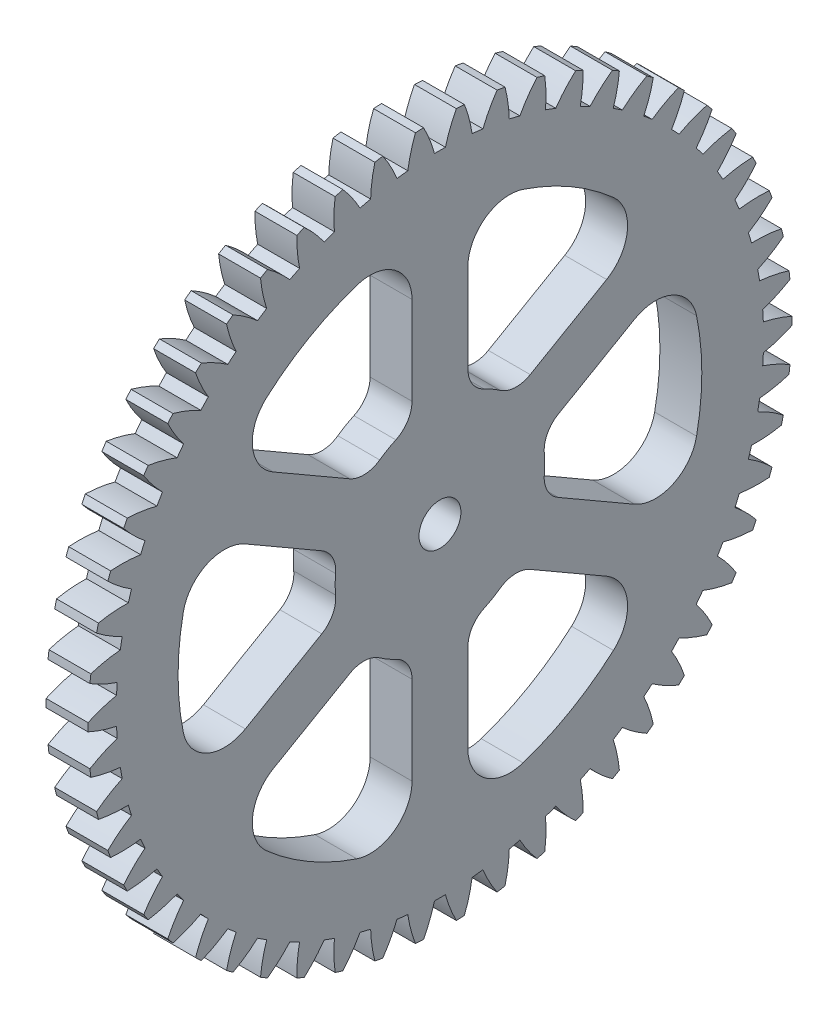
SolidWorks part; units mm, degrees
ref_plane "Plane1" through (0, 0, 0) normal (0, 0, 1) x (1, 0, 0)
ref_plane "Plane2" through (0, 0, 0) normal (0, 1, 0) x (1, 0, 0)
ref_plane "Plane3" through (0, 0, 0) normal (1, 0, 0) x (0, 0, -1)
sketch "HoldingSke" plane through (0, 0, 0) normal (0, 1, 0) x (1, 0, 0)
  line L0 (0, 0) -> (0.6531, -0.8989)
  line L1 (-15, 0) -> (100, 0) construction
  line L2 (0, 0) -> (-2.1039, 2.3779)
  line L3 (0, 0) -> (-11.863, 4.5341)
  line L4 (0, 0) -> (5.0761, 6.9867)
  line L5 (0, 0) -> (-46.8476, -17.4728)
  line L6 (0, 0) -> (-2.4869, -1.6779)
  line L7 (-2.1039, 2.3779) -> (8.6588, 51.2066)
  line L8 (-76.2, 54.61) -> (-75.2, 54.61)
  line L9 (-71.009, 38.7566) -> (-53.1078, 45.2721)
  line L10 (-76.2, 71.12) -> (104.1128, 71.12)
  line L11 (0, 0) -> (-3, 0)
  line L12 (-76.2, 101.6) -> (-76.166, 101.6)
  line L13 (24.9733, 27.94) -> (52.9518, 28.4284)
  line L14 (24.9733, 27.94) -> (24.9743, 27.94)
  line L15 (24.9733, 27.94) -> (100.4006, 29.5858)
  line L16 (-63.627, -0.9) -> (-12.827, -0.9)
  circle A0 centre (0, 0) radius 3
  circle A1 centre (0, 0) radius 23.174
  circle A2 centre (0, 0) radius 37.5
  circle A3 centre (0, 0) radius 3
  dimension "MHD" = 46.348
  dimension "Hub_dia" = 75
  dimension "Bore" = 6
  dimension "MBD" = 6
  dimension "Num_teeth" = 54
  dimension "Pitch" = 1.1111
  dimension "Overall_len" = 50
  dimension "Show_teeth" = 54
  dimension "Thickness" = 3
  dimension "OAL" = 50.0008
  dimension "T_dim" = 1
  dimension "Ap" = 20
  dimension "H" = 19.05
  dimension "Pitch_radius" = 180.3128
  dimension "Width" = 3
  dimension "Backlash" = 0.034
  dimension "Addendum_fac" = 1
  dimension "Dedendum_fac" = 1.25
  dimension "Clearance_fac" = 0.25
  dimension "Dedendum_add" = 0.001
  dimension "Module" = 0.9
sketch "BasProSke" plane through (0, 0, 0) normal (0, 1, 0) x (1, 0, 0)
  line L0 (-10, 0) -> (60, 0) construction
  line L1 (0, 0) -> (0, 25.2)
  line L2 (0, 0) -> (3, 0)
  line L3 (3, 0) -> (3, 25.2)
  line L4 (3, 25.2) -> (0, 25.2)
  dimension "Thickness" = 3
  dimension "Diameter" = 50.4
revolve "Base-Revolve" add sketch "BasProSke" angle 360 about L0
sketch "TooCutSke" plane through (0, 0, 0) normal (1, 0, 0) x (0, 0, -1)
  line L1 (0, 0) -> (0, 107) construction
  line L2 (0, 0) -> (-0.7663, 24.2879) construction
  line L3 (0, 0) -> (-2.8248, 48.5006) construction
  line L4 (-0.7663, 24.2879) -> (-1.4124, 24.2503) construction
  arc A0 (0.3905, 23.1707) -> (-0.3905, 23.1707) centre (0, 0) ccw
  arc A1 (1.1907, 25.1973) -> (-1.1907, 25.1973) centre (0, 0) ccw
  circle A2 centre (0, 0) radius 24.3 construction
  circle A3 centre (0, 0) radius 22.8345 construction
  arc A4 (-0.3905, 23.1707) -> (-1.1907, 25.1973) centre (-9.7744, 20.6368) ccw
  arc A5 (1.1907, 25.1973) -> (0.3905, 23.1707) centre (9.7744, 20.6368) ccw
  dimension "Root_dia" = 46.348
  dimension "Overcut_dia" = 50.4508
  dimension "Pitch_dia" = 48.6
  dimension "Base_dia" = 45.6691
  dimension "Flank_rad" = 9.72
  dimension "Half_ang" = 3.333
  dimension "Half_CT" = 0.6473
extrude "ToothCut" cut sketch "TooCutSke" along normal through all
fillet "Breaks" [suppressed] radius 0.018
fillet "RootFillets" [suppressed] radius 0.226
pattern_circular "TeethCuts" count 54 every 6.667 about axis through (-10, 0, 0) along (1, 0, 0) of "ToothCut", "RootFillets", "Breaks"
sketch "HubNeaOneSke" plane through (0, 0, 0) normal (-1, 0, 0) x (0, 0, 1)
  circle A0 centre (0, 0) radius 23.174
  dimension "Diameter" = 46.348
extrude "HubNearOne" [suppressed] add sketch "HubNeaOneSke" along normal blind 47.0008
sketch "HubNeaBotSke" plane through (0, 0, 0) normal (-1, 0, 0) x (0, 0, 1)
  circle A0 centre (0, 0) radius 23.174
  dimension "Diameter" = 46.348
extrude "HubNearBoth" [suppressed] add sketch "HubNeaBotSke" along normal blind 23.5004
ref_plane "FarPln" through (3, 0, 0) normal (1, 0, 0) x (0, 0, -1)
sketch "HubFarSke" plane through (3, 0, 0) normal (1, 0, 0) x (0, 0, -1)
  circle A0 centre (0, 0) radius 23.174
  dimension "Diameter" = 46.348
extrude "HubFar" [suppressed] add sketch "HubFarSke" along normal blind 23.5004
sketch "KeySke" plane through (0, 0, 0) normal (1, 0, 0) x (0, 0, -1)
  line L0 (-1, 0) -> (-1, 4)
  line L1 (-1, 4) -> (1, 4)
  line L2 (1, 4) -> (1, 0)
  line L3 (0, 0) -> (0, 34) construction
  line L4 (-1, 0) -> (1, 0)
  dimension "Offset" = 4
  dimension "Width" = 2
extrude "Keyway" [suppressed] cut sketch "KeySke" along normal mid plane 100.0016
pattern_circular "Keyway2" [suppressed] count 2 every 90 about axis through (-10, 0, 0) along (1, 0, 0)
sketch "Sketch1" plane through (3, 0, 0) normal (1, 0, 0) x (0, 0, -1)
  circle A0 centre (0, 0) radius 1.5
  dimension "D1" = 3
extrude "Cut-Extrude1" cut sketch "Sketch1" against normal through all
sketch "Sketch2" plane through (3, 0, 0) normal (1, 0, 0) x (0, 0, -1)
  line L0 (-2, 18.643) -> (-2, 7.2284)
  line L3 (-5.26, 5.3463) -> (-15.1453, 11.0536)
  arc A1 (-2, 7.2284) -> (-5.26, 5.3463) centre (0, 0) ccw
  arc A2 (-2, 18.643) -> (-15.1453, 11.0536) centre (0, 0) ccw
  dimension "D1" = 37.5
  dimension "D3" = 15
  dimension "D4" = 2
extrude "Cut-Extrude2" cut sketch "Sketch2" against normal through all
fillet "Fillet1" radius 2 2 edges at (1.5, 5.3463, 5.26) (1.5, 7.2284, 2)
fillet "Fillet2" radius 3 2 edges at (1.5, 11.0536, 15.1453) (1.5, 18.643, 2)
pattern_circular "CirPattern2" count 6 every 60 about axis through (0, 0, 0) along (1, 0, 0) of "Fillet2", "Fillet1", "Cut-Extrude2"
equation "' \"Module@HoldingSke\" = 6.35"
equation "' \"Num_teeth@HoldingSke\" = 12"
equation "' \"Ap@HoldingSke\" =  20"
equation "' \"Ap@HoldingSke\" = 20"
equation "' \"Width@HoldingSke\" = 0.5 * 25.4"
equation "' \"Hub_dia@HoldingSke\"= 1 * 25.4"
equation "' \"Hub_dia@HoldingSke\" = 1 * 25.4"
equation "' \"Overall_len@HoldingSke\" = 1.0 * 25.4"
equation "' \"Bore@HoldingSke\" = 0.75 * 25.4"
equation "' \"T_dim@HoldingSke\" = 0.1 * 25.4"
equation "' \"Width@KeySke\" = 0.25 * 25.4"
equation "' \"Show_teeth@HoldingSke\" = 13"
equation "' \"Backlash@HoldingSke\" = 0.009 * 25.4"
equation "' \"Addendum_fac@HoldingSke\" = 1.0"
equation "' \"Dedendum_fac@HoldingSke\" = 1.25"
equation "' \"Dedendum_add@HoldingSke\" = 0.00005 * 25.4"
equation "' \"Clearance_fac@HoldingSke\" = 0.25"
equation "\"Pitch@HoldingSke\" = 1 / \"Module@HoldingSke\""
equation "\"Overcut_dia@TooCutSke\" = (\"Num_teeth@HoldingSke\" + 2 * \"Addendum_fac@HoldingSke\") / \"Pitch@HoldingSke\" + 0.002 * 25.4"
equation "\"Pitch_dia@TooCutSke\" = \"Num_teeth@HoldingSke\" / \"Pitch@HoldingSke\""
equation "\"Base_dia@TooCutSke\" = \"Num_teeth@HoldingSke\" / \"Pitch@HoldingSke\" * cos((\"Ap@HoldingSke\"  * 3.14159265 / 180))"
equation "\"Root_dia@TooCutSke\" = (\"Num_teeth@HoldingSke\" + 2) / \"Pitch@HoldingSke\" - 2 * (\"Addendum_fac@HoldingSke\" + \"Dedendum_fac@HoldingSke\") / \"Pitch@HoldingSke\" - \"Dedendum_add@HoldingSke\" * 2"
equation "\"Half_ang@TooCutSke\" = 180 / \"Num_teeth@HoldingSke\""
equation "\"Half_CT@TooCutSke\" = \"Num_teeth@HoldingSke\" / \"Pitch@HoldingSke\" * sin((3.14159265 / 2 / \"Num_teeth@HoldingSke\")) / 2 - 7 * \"Backlash@HoldingSke\" / 4"
equation "\"Flank_rad@TooCutSke\" = \"Num_teeth@HoldingSke\" / \"Pitch@HoldingSke\" / 5"
equation "\"Radius@RootFillets\" = \"Clearance_fac@HoldingSke\" / \"Pitch@HoldingSke\" + \"Dedendum_add@HoldingSke\""
equation "\"Break_rad@Breaks\" = 0.02 / \"Pitch@HoldingSke\""
equation "\"Thickness@HoldingSke\" = \"Width@HoldingSke\""
equation "\"OAL@HoldingSke\" = \"Thickness@HoldingSke\""
equation "\"MHD@HoldingSke\" = (\"Num_teeth@HoldingSke\" + 2) / \"Pitch@HoldingSke\" - 2 * (\"Addendum_fac@HoldingSke\" + \"Dedendum_fac@HoldingSke\")  / \"Pitch@HoldingSke\" - \"Dedendum_add@HoldingSke\" * 2"
equation "\"MBD@HoldingSke\" = (\"Num_teeth@HoldingSke\" + 2) / \"Pitch@HoldingSke\" - 2 * (\"Addendum_fac@HoldingSke\" + \"Dedendum_fac@HoldingSke\")  / \"Pitch@HoldingSke\" - \"Dedendum_add@HoldingSke\" * 2 - 0.002 * 25.4"
equation "\"MHD@HoldingSke\" = ((sgn( \"MHD@HoldingSke\" - \"Hub_dia@HoldingSke\" )-1)*( \"MHD@HoldingSke\" - \"Hub_dia@HoldingSke\" ))/-2+ \"Hub_dia@HoldingSke\""
equation "\"MBD@HoldingSke\" = ((sgn( \"MBD@HoldingSke\" - \"Bore@HoldingSke\" )-1)*( \"MBD@HoldingSke\" - \"Bore@HoldingSke\" ))/-2+ \"Bore@HoldingSke\""
equation "\"OAL@HoldingSke\" = ((sgn( \"OAL@HoldingSke\" - \"Overall_len@HoldingSke\" )+1)*( \"OAL@HoldingSke\" - \"Overall_len@HoldingSke\" ))/2 + \"Overall_len@HoldingSke\" + 0.000002 * 25.4"
equation "\"Num_teeth@TeethCuts\" = int( \"Show_teeth@HoldingSke\" ) + 1"
equation "\"Num_teeth@TeethCuts\" = ((sgn( \"Num_teeth@TeethCuts\" - \"Num_teeth@HoldingSke\" )-1)*( \"Num_teeth@TeethCuts\" - \"Num_teeth@HoldingSke\" ))/-2+ \"Num_teeth@HoldingSke\""
equation "\"Num_teeth@TeethCuts\" = ((sgn( \"Num_teeth@TeethCuts\" - 2.0)+1)*( \"Num_teeth@TeethCuts\" - 2.0))/2 +2.0"
equation "\"Angle@TeethCuts\" = 360.0 / \"Num_teeth@HoldingSke\""
equation "\"Diameter@BasProSke\" = (\"Num_teeth@HoldingSke\" + 2 * \"Addendum_fac@HoldingSke\") / \"Pitch@HoldingSke\""
equation "\"Thickness@BasProSke\"  = \"Thickness@HoldingSke\""
equation "' \"Fillet_rad@BasProSke\" =  \"Thickness@HoldingSke\" * 0.05"
equation "' \"Fillet_rad@BasProSke\" = \"Thickness@HoldingSke\" * 0.05"
equation "\"MHD@HoldingSke\" = ((sgn( \"MHD@HoldingSke\" - \"Root_dia@TooCutSke\" )-1)*( \"MHD@HoldingSke\" - \"Root_dia@TooCutSke\" ))/-2+ \"Root_dia@TooCutSke\""
equation "\"Diameter@HubNeaOneSke\" = \"MHD@HoldingSke\""
equation "\"Length@HubNearOne\" = \"OAL@HoldingSke\" - \"Thickness@BasProSke\""
equation "\"Diameter@HubNeaBotSke\" = \"MHD@HoldingSke\""
equation "\"Length@HubNearBoth\" = ( \"OAL@HoldingSke\" - \"Thickness@BasProSke\" ) / 2.0"
equation "\"Thickness@FarPln\" = \"Thickness@BasProSke\""
equation "\"Diameter@HubFarSke\" = \"MHD@HoldingSke\""
equation "\"Length@HubFar\" = ( \"OAL@HoldingSke\" - \"Thickness@BasProSke\" ) / 2.0"
equation "\"D1@Keyway\" = \"OAL@HoldingSke\" * 2.0"
equation "\"Offset@KeySke\" = \"T_dim@HoldingSke\" + \"MBD@HoldingSke\" / 2.0"
